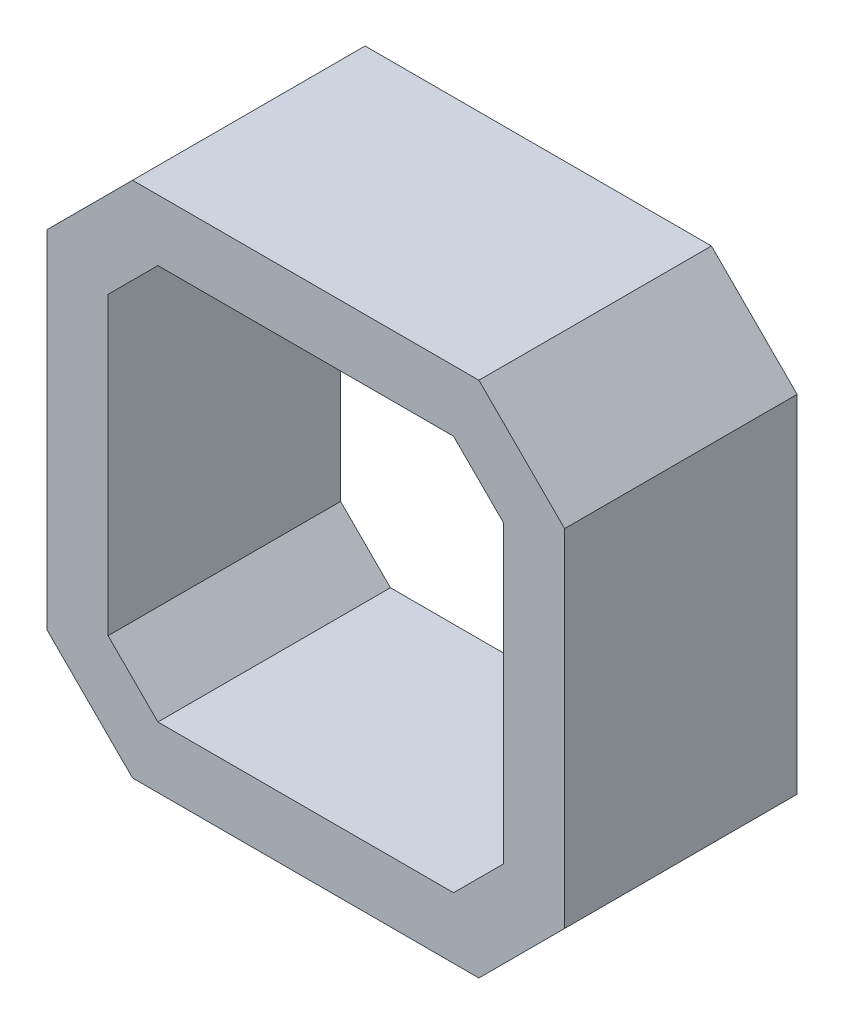
SolidWorks part; units mm, degrees
ref_plane "Front Plane" through (0, 0, 0) normal (0, 0, 1) x (1, 0, 0)
ref_plane "Top Plane" through (0, 0, 0) normal (0, 1, 0) x (1, 0, 0)
ref_plane "Right Plane" through (0, 0, 0) normal (1, 0, 0) x (0, 0, -1)
sketch "Sketch1" plane through (0, 0, 0) normal (0, 0, 1) x (1, 0, 0)
  line L0 (-21.15, 14.15) -> (-14.15, 21.15)
  line L1 (-14.15, -21.15) -> (14.15, -21.15)
  line L2 (-21.15, -14.15) -> (-21.15, 14.15)
  line L3 (-14.15, 21.15) -> (14.15, 21.15)
  line L4 (21.15, -14.15) -> (21.15, 14.15)
  line L5 (-21.15, -21.15) -> (21.15, 21.15) construction
  line L6 (-21.15, 21.15) -> (21.15, -21.15) construction
  line L7 (14.15, 21.15) -> (21.15, 14.15)
  line L8 (14.15, -21.15) -> (21.15, -14.15)
  line L9 (-21.15, -14.15) -> (-14.15, -21.15)
  line L10 (-12.0789, 16.15) -> (12.0789, 16.15)
  line L11 (12.0789, 16.15) -> (16.15, 12.0789)
  line L12 (16.15, -12.0789) -> (16.15, 12.0789)
  line L13 (12.0789, -16.15) -> (16.15, -12.0789)
  line L14 (-12.0789, -16.15) -> (12.0789, -16.15)
  line L15 (-16.15, -12.0789) -> (-12.0789, -16.15)
  line L16 (-16.15, -12.0789) -> (-16.15, 12.0789)
  line L17 (-16.15, 12.0789) -> (-12.0789, 16.15)
  point P0 (0, 0)
  dimension "D1" = 42.3
  dimension "D2" = 5
extrude "Boss-Extrude1" add sketch "Sketch1" along normal blind 19
